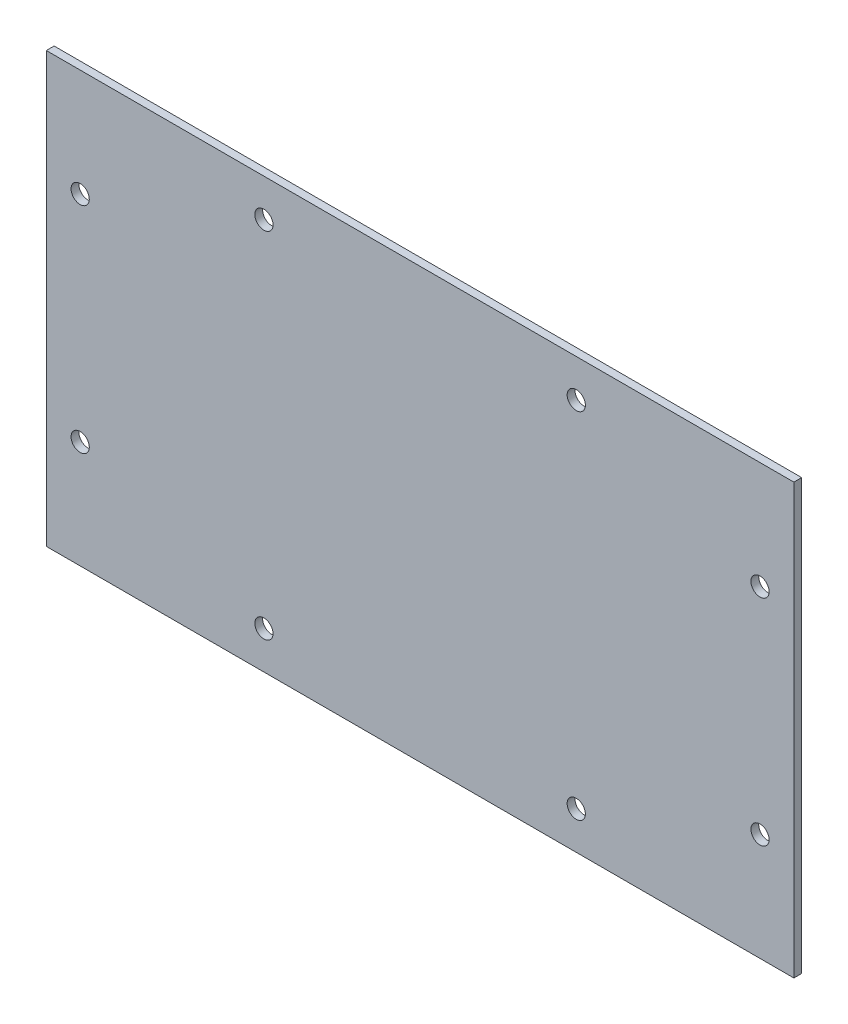
SolidWorks part; units mm, degrees
ref_plane "Front Plane" through (0, 0, 0) normal (0, 0, 1) x (1, 0, 0)
ref_plane "Top Plane" through (0, 0, 0) normal (0, 1, 0) x (1, 0, 0)
ref_plane "Right Plane" through (0, 0, 0) normal (1, 0, 0) x (0, 0, -1)
sketch "Sketch2" plane through (0, 0, 0) normal (0, 0, 1) x (1, 0, 0)
  line L0 (-143.6, 82.5) -> (143.6, 82.5)
  line L1 (-143.6, 82.5) -> (-143.6, -82.5)
  line L2 (-143.6, -82.5) -> (143.6, -82.5)
  line L3 (143.6, 82.5) -> (143.6, -82.5)
  line L4 (-130.6, 82.5) -> (-130.6, -82.5) construction
  line L5 (130.6, 82.5) -> (130.6, -82.5) construction
  line L6 (-221.8231, 0) -> (195.359, 0) construction
  line L7 (0, 110.3217) -> (0, -104.6083) construction
  circle A0 centre (-130.6, 41.25) radius 3.5
  circle A1 centre (-130.6, -41.25) radius 3.5
  circle A2 centre (130.6, -41.25) radius 3.5
  circle A3 centre (130.6, 41.25) radius 3.5
  point P8 (0, 82.5)
  point P10 (-143.6, 0)
  dimension "D5" = 7
  dimension "D1" = 287.2
  dimension "D2" = 165
  dimension "D3" = 13
  dimension "D4" = 13
  dimension "D6" = 41.25
extrude "Boss-Extrude2" add sketch "Sketch2" along normal blind 3
sketch "Sketch3" plane through (0, 0, 3) normal (0, 0, 1) x (1, 0, 0)
  line L0 (0, 104.3637) -> (0, -151.0086) construction
  line L1 (-60, 68) -> (60, 68) construction
  line L2 (-60, 68) -> (-60, -68) construction
  line L3 (-60, -68) -> (60, -68) construction
  line L4 (60, 68) -> (60, -68) construction
  line L5 (-222.3182, 0) -> (190.103, 0) construction
  circle A0 centre (-60, 68) radius 3.5
  circle A1 centre (60, 68) radius 3.5
  circle A2 centre (60, -68) radius 3.5
  circle A3 centre (-60, -68) radius 3.5
  point P4 (0, 68)
  point P6 (-60, 0)
  dimension "D3" = 7
  dimension "D1" = 120
  dimension "D2" = 136
extrude "Cut-Extrude1" cut sketch "Sketch3" against normal blind 3
